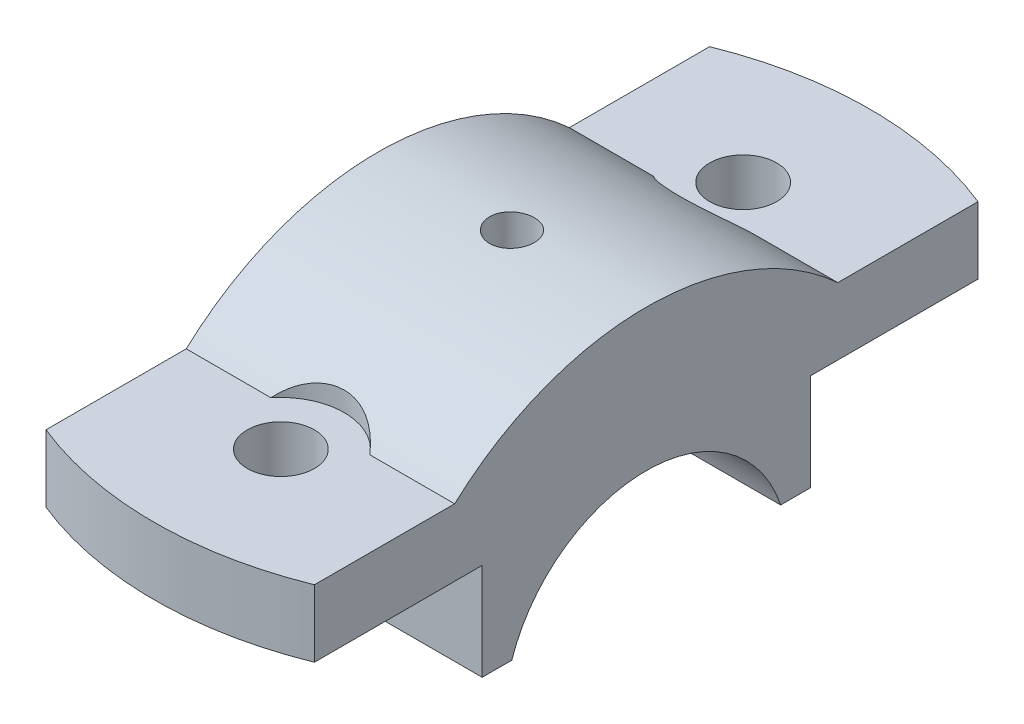
SolidWorks part; units mm, degrees
ref_plane "Front Plane" through (0, 0, 0) normal (0, 0, 1) x (1, 0, 0)
ref_plane "Top Plane" through (0, 0, 0) normal (0, 1, 0) x (1, 0, 0)
ref_plane "Right Plane" through (0, 0, 0) normal (1, 0, 0) x (0, 0, -1)
sketch "Sketch1" plane through (0, 0, 0) normal (1, 0, 0) x (0, 0, -1)
  line L0 (0, 127.7394) -> (0, -72.2606) construction
  line L1 (0, 0) -> (80.8139, 0) construction
  line L2 (22, 6) -> (22, 19)
  line L3 (18.0278, 6) -> (22, 6)
  line L4 (22, 19) -> (50, 19)
  line L5 (50, 19) -> (50, 28)
  line L6 (50, 28) -> (25.6905, 28)
  line L7 (-50, 28) -> (-25.6905, 28)
  line L8 (-50, 19) -> (-50, 28)
  line L9 (-22, 19) -> (-50, 19)
  line L10 (-18.0278, 6) -> (-22, 6)
  line L11 (-22, 6) -> (-22, 19)
  arc A0 (18.0278, 6) -> (-18.0278, 6) centre (0, 0) ccw
  arc A2 (25.6905, 28) -> (-25.6905, 28) centre (0, 0) ccw
  dimension "D1" = 19
  dimension "D5" = 50
  dimension "D6" = 200
  dimension "D7" = 38
  dimension "D2" = 19
  dimension "D3" = 13
  dimension "D4" = 9
  dimension "D8" = 44
extrude "Boss-Extrude4" add sketch "Sketch1" along normal mid plane 36
sketch "Sketch5" plane through (0, 28, 0) normal (0, 1, 0) x (1, 0, 0)
  line L0 (-28.8965, 0) -> (35.905, 0) construction
  line L1 (18, 22) -> (18, 50) construction
  circle A0 centre (0, 31) radius 4.5
  circle A1 centre (0, -31) radius 4.5
  dimension "D1" = 9
  dimension "D2" = 31
  dimension "D3" = 18
extrude "Cut-Extrude4" cut sketch "Sketch5" against normal through all
sketch "Sketch7" plane through (0, 28, 0) normal (0, 1, 0) x (1, 0, 0)
  line L0 (-25.7742, 0) -> (34.5251, 0) construction
  line L1 (-18, -25.6905) -> (-18, -50) construction
  circle A0 centre (0, -31) radius 8.5
  circle A1 centre (0, 31) radius 8.5
  dimension "D1" = 17
  dimension "D2" = 31
  dimension "D3" = 18
extrude "Cut-Extrude6" cut sketch "Sketch7" along normal blind 45
sketch "Sketch8" plane through (0, 28, 0) normal (0, 1, 0) x (1, 0, 0)
  line L0 (-21.8673, 0) -> (32.1533, 0) construction
  line L1 (-18, -25.6905) -> (-18, -50) construction
  line L2 (18, -50) -> (-18, -50) construction
  line L3 (18, -25.6905) -> (18, -50) construction
  line L4 (-18, 50) -> (-18, 25.6905) construction
  line L5 (18, 50) -> (-18, 50) construction
  line L6 (18, 50) -> (18, 25.6905) construction
  line L7 (-18, -44.4972) -> (-18, -50)
  line L8 (18, -50) -> (-18, -50)
  line L9 (18, -44.4972) -> (18, -50)
  line L10 (-18, 50) -> (-18, 44.4972)
  line L11 (18, 50) -> (-18, 50)
  line L12 (18, 50) -> (18, 44.4972)
  arc A0 (-18, -44.4972) -> (18, -44.4972) centre (0, 0) ccw
  arc A1 (18, 44.4972) -> (-18, 44.4972) centre (0, 0) ccw
  dimension "D2" = 96
  dimension "D1" = 0
extrude "Cut-Extrude7" cut sketch "Sketch8" against normal blind 45
hole_wizard "CBORE for M5 Hex Head Bolt2" positions "3DSketch3" profile "Sketch11" counterbore size "M5" standard "ANSI Metric" end condition through all
sketch3d "3DSketch3"
  point P0 (0, 0, 0)
  point P4 (0, 38, 0)
  dimension "D1" = 0
  dimension "D2" = 0
sketch "Sketch11" plane through (0, 38, 0) normal (1, 0, 0) x (0, 0, 1)
  line L0 (0, 0) -> (0, 32)
  line L1 (0, 32) -> (2.5, 32)
  line L2 (2.5, 13.3001) -> (2.5, 32)
  line L3 (2.5, 13.3001) -> (2.9995, 13)
  line L4 (2.9995, 13) -> (3, 13)
  line L5 (3, 13) -> (3, 0)
  line L7 (0, 0) -> (3, 0)
  line L9 (-2.5, 13.3001) -> (-2.9995, 13) construction
  line L11 (0, -6.35) -> (0, 107.95) construction
  dimension "Thru Hole Dia." = 5
  dimension "Thru Hole Depth" = 32
  dimension "C'Bore Dia." = 6
  dimension "C'Bore Depth" = 13
  dimension "Mid C'Sink Dia." = 5.999
  dimension "Mid C'Sink Angle" = 118
